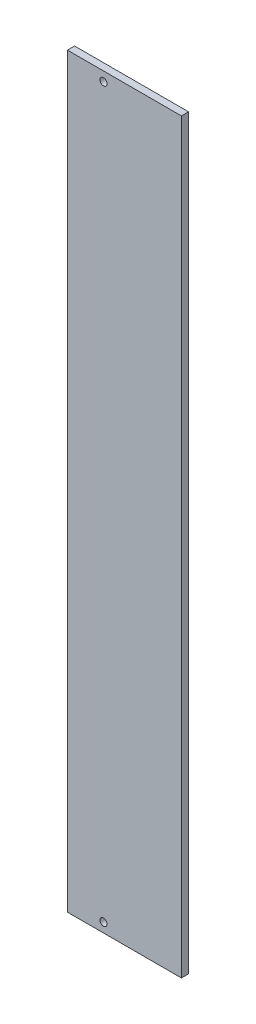
SolidWorks part; units mm, degrees
ref_plane "Front Plane" through (0, 0, 0) normal (0, 0, 1) x (1, 0, 0)
ref_plane "Top Plane" through (0, 0, 0) normal (0, 1, 0) x (1, 0, 0)
ref_plane "Right Plane" through (0, 0, 0) normal (1, 0, 0) x (0, 0, -1)
sketch "Sketch1" plane through (0, 0, 0) normal (0, 0, 1) x (1, 0, 0)
  line L0 (3.8, 262) -> (3.8, 0) construction
  line L1 (0, 0) -> (40, 0)
  line L2 (0, 0) -> (0, 262)
  line L3 (0, 262) -> (40, 262)
  line L4 (40, 0) -> (40, 262)
  line L5 (7.6, 262) -> (7.6, 0) construction
  line L6 (40, 4.2) -> (0, 4.2) construction
  line L8 (40, 18.75) -> (0, 18.75) construction
  line L9 (0, 243.4) -> (40, 243.4) construction
  line L10 (12.65, 262) -> (12.65, 0) construction
  circle A0 centre (12.65, 258.7) radius 1.25
  circle A1 centre (12.65, 3.3) radius 1.25
extrude "Boss-Extrude1" add sketch "Sketch1" along normal blind 2.5
